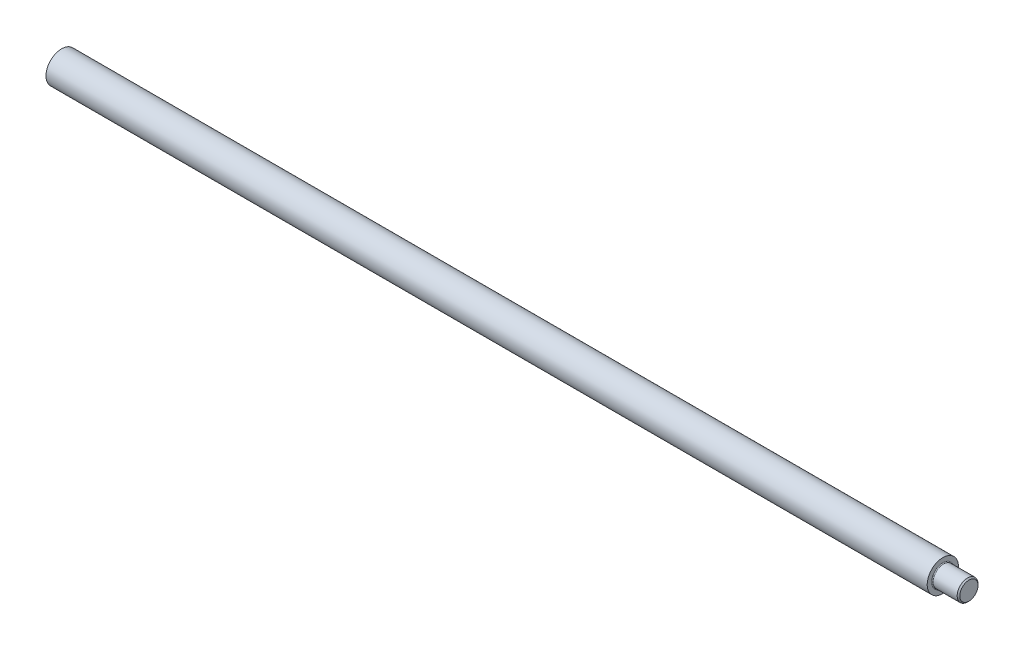
SolidWorks part; units mm, degrees
ref_plane "Piano frontale" through (0, 0, 0) normal (0, 0, 1) x (1, 0, 0)
ref_plane "Piano superiore" through (0, 0, 0) normal (0, 1, 0) x (1, 0, 0)
ref_plane "Piano destro" through (0, 0, 0) normal (1, 0, 0) x (0, 0, -1)
sketch "Sketch1" plane through (0, 0, 0) normal (0, 0, 1) x (1, 0, 0)
  line L0 (30, 5.6842) -> (30, 0)
  line L1 (30, 0) -> (360, 0)
  line L2 (360, 0) -> (360, 3.3158)
  line L3 (360, 3.3158) -> (359.5263, 3.7895)
  line L4 (359.5263, 3.7895) -> (350.8105, 3.7895)
  line L5 (350.5263, 4.0737) -> (350.5263, 5.6842)
  line L6 (350.5263, 5.6842) -> (30, 5.6842)
  line L7 (30, 0) -> (360, 0) construction
  arc A0 (350.8105, 3.7895) -> (350.5263, 4.0737) centre (350.8105, 4.0737) cw
  dimension "D1" = 330
revolve "Revolve1" add sketch "Sketch1" angle 360 about L7
